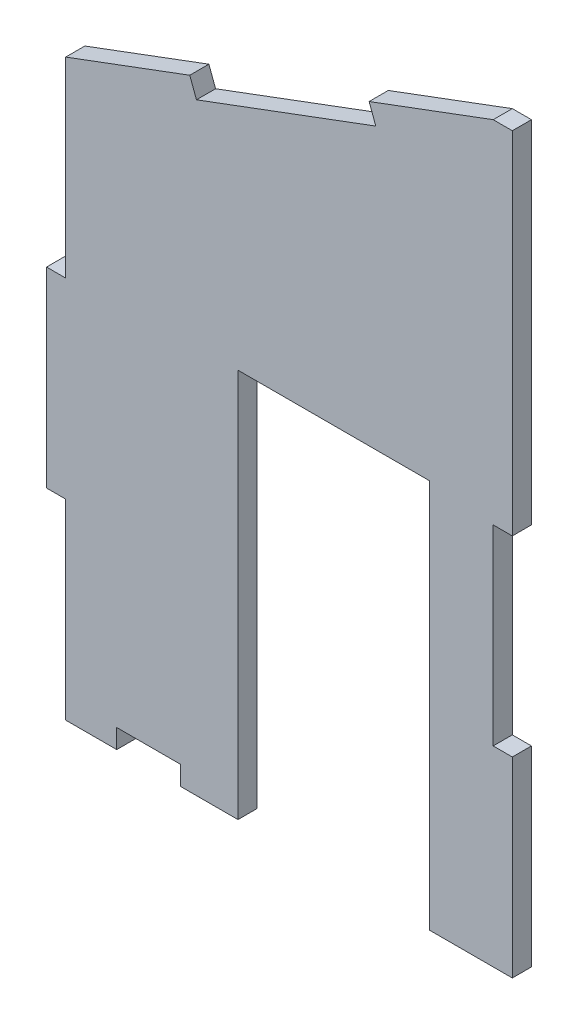
SolidWorks part; units mm, degrees
ref_plane "Front Plane" through (0, 0, 0) normal (0, 0, 1) x (1, 0, 0)
ref_plane "Top Plane" through (0, 0, 0) normal (0, 1, 0) x (1, 0, 0)
ref_plane "Right Plane" through (0, 0, 0) normal (1, 0, 0) x (0, 0, -1)
sketch "Model" plane through (0, 0, 0) normal (0, 0, 1) x (1, 0, 0)
  line L0 (178.6279, 199.1238) -> (178.6279, 169.1238)
  line L5 (181.6279, 139.1238) -> (189.6279, 139.1238)
  line L10 (251.6279, 199.1238) -> (251.6279, 254.1238) construction
  line L16 (248.6279, 199.1238) -> (248.6279, 254.1238) construction
  line L18 (248.6279, 254.1238) -> (229.1815, 246.8676)
  line L19 (248.6279, 254.1238) -> (251.6279, 254.1238)
  line L20 (189.6279, 139.1238) -> (189.6279, 142.1238)
  line L21 (249.6767, 251.313) -> (182.6767, 226.313) construction
  line L22 (189.6279, 142.1238) -> (199.6279, 142.1238)
  line L23 (181.6279, 229.1238) -> (182.6767, 226.313) construction
  line L29 (251.6279, 254.1238) -> (250.8864, 251.2168) construction
  line L33 (238.6279, 139.1238) -> (238.6279, 200.1238)
  line L34 (248.6279, 254.1238) -> (249.6767, 251.313) construction
  line L39 (199.6279, 142.1238) -> (199.6279, 139.1238)
  line L41 (238.6279, 200.1238) -> (208.6279, 200.1238)
  line L42 (208.6279, 200.1238) -> (208.6279, 139.1238)
  line L43 (208.6279, 139.1238) -> (181.6279, 139.1238) construction
  line L45 (251.6279, 169.1238) -> (248.6279, 169.1238)
  line L46 (248.6279, 169.1238) -> (248.6279, 199.1238)
  line L47 (248.6279, 199.1238) -> (251.6279, 199.1238)
  line L49 (215.1279, 241.6238) -> (216.1767, 238.813) construction
  line L50 (201.0744, 236.3799) -> (202.1232, 233.5692)
  line L51 (229.1815, 246.8676) -> (230.2302, 244.0569)
  line L52 (201.0744, 236.3799) -> (181.6279, 229.1238)
  line L53 (230.2302, 244.0569) -> (202.1232, 233.5692)
  line L54 (248.6279, 254.1238) -> (181.6279, 229.1238) construction
  line L57 (199.6279, 139.1238) -> (208.6279, 139.1238)
  line L59 (251.6279, 254.1238) -> (251.6279, 199.1238)
  line L60 (251.6279, 169.1238) -> (251.6279, 139.1238)
  line L61 (251.6279, 251.0277) -> (250.8864, 251.2168) construction
  line L62 (251.6279, 229.1238) -> (181.6279, 229.1238) construction
  line L312 (251.6279, 139.1238) -> (238.6279, 139.1238)
  line L313 (181.6279, 139.1238) -> (181.6279, 169.1238)
  line L314 (181.6279, 169.1238) -> (178.6279, 169.1238)
  line L332 (178.6279, 199.1238) -> (181.6279, 199.1238)
  line L333 (181.6279, 199.1238) -> (181.6279, 229.1238)
  point P4 (348.8864, 226.2168)
  point P6 (265.1905, 254.1238)
  point P7 (178.1905, 232.3738)
  point P9 (352.1905, 232.3738)
  point P37 (248.6279, 184.1238)
  point P349 (349.6279, 229.1238)
  dimension "D5" = 10
  dimension "D3" = 30
  dimension "D4" = 3
  dimension "6" = 3
  dimension "D6" = 8
  dimension "D7" = 30
  dimension "D8" = 30
  dimension "D9" = 9
  dimension "D10" = 55
  dimension "D11" = 30
  dimension "D12" = 3
  dimension "D13" = 3
  dimension "D14" = 20.7561
  dimension "D15" = 20.7561
  dimension "D16" = 3
  dimension "D17" = 30
  dimension "D25" = 30
  dimension "D27" = 3
  dimension "D28" = 10
  dimension "D29" = 30
extrude "Boss-Extrude1" add sketch "Model" along normal blind 3
